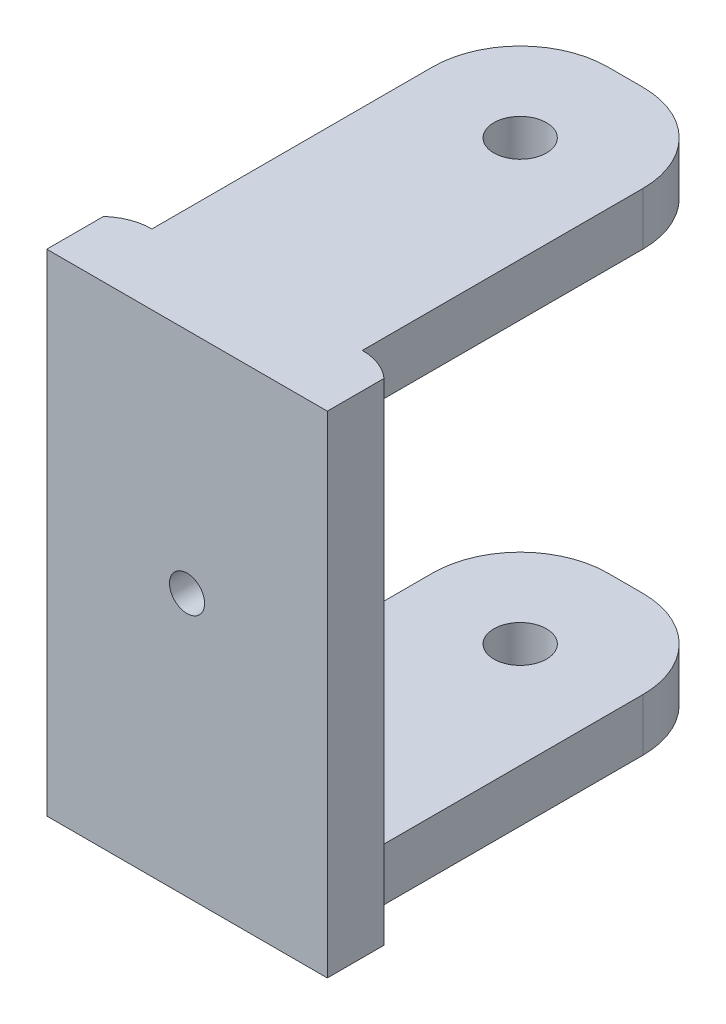
SolidWorks part; units mm, degrees
ref_plane "前视基准面" through (0, 0, 0) normal (0, 0, 1) x (1, 0, 0)
ref_plane "上视基准面" through (0, 0, 0) normal (0, 1, 0) x (1, 0, 0)
ref_plane "右视基准面" through (0, 0, 0) normal (1, 0, 0) x (0, 0, -1)
sketch "草图1" plane through (0, 0, 0) normal (0, 1, 0) x (1, 0, 0)
  line L1 (-5.0261, 12.8707) -> (-3.0261, 12.8707)
  line L2 (-10.0261, 7.8707) -> (-10.0261, -8.1293)
  line L3 (-10.0261, -8.1293) -> (1.9739, -8.1293)
  line L4 (1.9739, 7.8707) -> (1.9739, -8.1293)
  arc A0 (-3.0261, 12.8707) -> (1.9739, 7.8707) centre (-3.0261, 7.8707) cw
  arc A1 (-5.0261, 12.8707) -> (-10.0261, 7.8707) centre (-5.0261, 7.8707) ccw
  point P4 (1.9739, -0.1293)
  dimension "D3" = 5
  dimension "D1" = 12
  dimension "D2" = 21
extrude "凸台-拉伸2" add sketch "草图1" along normal mid plane 28
sketch "草图2" plane through (0, 0, 0) normal (0, 1, 0) x (1, 0, 0)
  line L0 (-10.0261, 7.8707) -> (-10.0261, -8.1293) construction
  line L1 (-10.0261, -8.1293) -> (1.9739, -8.1293)
  line L2 (-13.0261, -11.1293) -> (-13.0261, -12.1293)
  line L3 (-13.0261, -12.1293) -> (4.9739, -12.1293)
  line L4 (4.9739, -11.1293) -> (4.9739, -12.1293)
  line L7 (1.9739, -8.1293) -> (1.9739, 7.8707) construction
  line L8 (-10.0261, -8.1293) -> (1.9739, -8.1293) construction
  arc A0 (1.9739, -8.1293) -> (4.9739, -11.1293) centre (1.9739, -11.1293) cw
  arc A1 (-10.0261, -8.1293) -> (-13.0261, -11.1293) centre (-10.0261, -11.1293) ccw
  dimension "D4" = 3
  dimension "D1" = 3
  dimension "D2" = 3
  dimension "D3" = 4
sketch "草图4" plane through (0, 0, 0) normal (0, 1, 0) x (1, 0, 0)
  line L0 (-4.0261, 13.6576) -> (-4.0261, -15.93) construction
  line L1 (1.9739, -8.1293) -> (1.9739, 7.8707) construction
  line L2 (-18.9669, 6.8707) -> (12.9729, 6.8707) construction
  line L3 (-3.0261, 12.8707) -> (-5.0261, 12.8707) construction
  circle A0 centre (-4.0261, 6.8707) radius 1.5
  dimension "D3" = 3
  dimension "D1" = 6
  dimension "D2" = 6
extrude "切除-拉伸2" cut sketch "草图4" against normal mid plane 42
extrude "凸台-拉伸3" add sketch "草图2" along normal mid plane 28
sketch "草图5" plane through (0, 0, 0) normal (0, 1, 0) x (1, 0, 0)
  line L1 (-10.0261, -8.1293) -> (1.9739, -8.1293)
  line L2 (-10.0261, -8.1293) -> (-10.0261, 18.6795)
  line L3 (-10.0261, 18.6795) -> (1.9739, 18.6795)
  line L4 (1.9739, -8.1293) -> (1.9739, 18.6795)
extrude "切除-拉伸3" cut sketch "草图5" against normal mid plane 22
sketch "草图7" plane through (0, 0, 12.1293) normal (0, 0, 1) x (1, 0, 0)
  line L0 (12.5118, 1) -> (-19.2589, 1) construction
  line L1 (-4.0261, 15.7136) -> (-4.0261, -16.0571) construction
  line L2 (4.9739, 14) -> (4.9739, -14) construction
  line L3 (-10.0261, -14) -> (-5.0261, -14) construction
  circle A0 centre (-4.0261, 1) radius 1
  dimension "D3" = 2
  dimension "D1" = 9
  dimension "D2" = 15
extrude "切除-拉伸4" cut sketch "草图7" along normal mid plane 22
sketch "草图8" plane through (0, 0, 8.1293) normal (0, 0, -1) x (-1, 0, 0)
  circle A0 centre (4.0261, 1) radius 2
  dimension "D1" = 4
extrude "切除-拉伸5" cut sketch "草图8" against normal blind 1
sketch "草图9" plane through (0, 0, 12.1293) normal (0, 0, 1) x (1, 0, 0)
  line L0 (-13.0261, -14) -> (4.9739, -14) construction
  line L1 (-13.0261, 14) -> (-12.0261, 14)
  line L2 (-13.0261, 14) -> (-13.0261, -14)
  line L3 (-13.0261, -14) -> (-12.0261, -14)
  line L4 (-12.0261, 14) -> (-12.0261, -14)
  line L6 (4.9739, 14) -> (3.9739, 14)
  line L7 (4.9739, 14) -> (4.9739, -14)
  line L8 (4.9739, -14) -> (3.9739, -14)
  line L9 (3.9739, 14) -> (3.9739, -14)
  dimension "D1" = 1
  dimension "D2" = 1
extrude "切除-拉伸6" cut sketch "草图9" against normal blind 10
